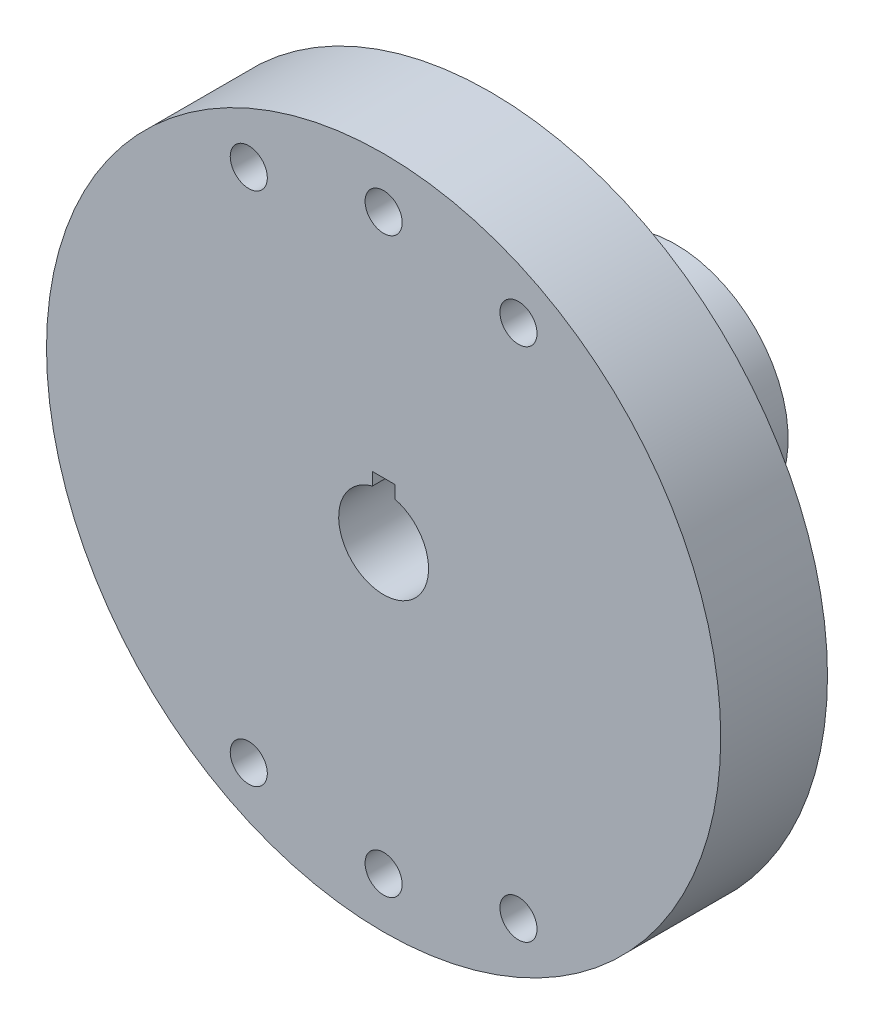
SolidWorks part; units mm, degrees
ref_plane "Front Plane" through (0, 0, 0) normal (0, 0, 1) x (1, 0, 0)
ref_plane "Top Plane" through (0, 0, 0) normal (0, 1, 0) x (1, 0, 0)
ref_plane "Right Plane" through (0, 0, 0) normal (1, 0, 0) x (0, 0, -1)
ref_plane "Plane1" through (0, 0, 0) normal (0, -1, 0) x (1, 0, 0)
sketch "Sketch1" plane through (0, 0, 0) normal (0, -1, 0) x (1, 0, 0)
  line L0 (30, 10) -> (0, 10)
  line L1 (0, 10) -> (0, 0.5)
  line L2 (0, 0.5) -> (30, 0.5)
  line L3 (30, 0.5) -> (30, 10)
  line L4 (0, 10) -> (0, 0.5) construction
revolve "Revolve1" add sketch "Sketch1" angle 360 about L4
sketch "Sketch2" plane through (0, 0, 0.5) normal (0, 0, -1) x (-1, 0, 0)
  arc A0 (1.9019, -26.9329) -> (10.5623, -24.8483) centre (0, 0) ccw
  arc A1 (10.5623, -24.8483) -> (14.3793, -22.8525) centre (12, -22.95) ccw
  arc A2 (14.3793, -22.8525) -> (14.3793, 22.8525) centre (0, 0) ccw
  arc A3 (14.3793, 22.8525) -> (10.5623, 24.8483) centre (12, 22.95) ccw
  arc A4 (10.5623, 24.8483) -> (1.9019, 26.9329) centre (0, 0) ccw
  arc A5 (1.9019, 26.9329) -> (-1.9019, 26.9329) centre (0, 25.5) ccw
  arc A6 (-1.9019, 26.9329) -> (-10.5623, 24.8483) centre (0, 0) ccw
  arc A7 (-10.5623, 24.8483) -> (-14.3793, 22.8525) centre (-12, 22.95) ccw
  arc A8 (-14.3793, 22.8525) -> (-14.3793, -22.8525) centre (0, 0) ccw
  arc A9 (-14.3793, -22.8525) -> (-10.5623, -24.8483) centre (-12, -22.95) ccw
  arc A10 (-10.5623, -24.8483) -> (-1.9019, -26.9329) centre (0, 0) ccw
  arc A11 (-1.9019, -26.9329) -> (1.9019, -26.9329) centre (0, -25.5) ccw
extrude "Cut-Extrude1" cut sketch "Sketch2" against normal blind 3.5
sketch "Sketch3" plane through (0, 0, 4) normal (0, 0, -1) x (-1, 0, 0)
  circle A0 centre (0, 0) radius 17.4
extrude "Boss-Extrude1" add sketch "Sketch3" along normal blind 4
sketch "Sketch4" plane through (0, 0, 0) normal (0, 0, -1) x (-1, 0, 0)
  circle A0 centre (0, 0) radius 10
extrude "Boss-Extrude2" add sketch "Sketch4" along normal blind 16
sketch "Sketch5" plane through (0, 0, 10) normal (0, 0, 1) x (1, 0, 0)
  line L0 (1, 5) -> (-1, 5)
  line L1 (-1, 5) -> (-1, 3.873)
  line L2 (1, 3.873) -> (1, 5)
  arc A0 (-1, 3.873) -> (1, 3.873) centre (0, 0) cw
extrude "Cut-Extrude2" cut sketch "Sketch5" against normal through all
sketch "Sketch6" plane through (0, 0, 0) normal (0, -1, 0) x (1, 0, 0)
  line L0 (4, 10) -> (0, 10)
  line L1 (0, 10) -> (0, -16)
  line L2 (0, -16) -> (4, -16)
  line L3 (4, -16) -> (4, 10)
  line L4 (0, 10) -> (0, -16) construction
revolve "Cut-Revolve1" cut sketch "Sketch6" angle 360 about L4
hole_wizard "#4 Clearance Hole1" positions "Sketch8" profile "Sketch7" hole size "#4" standard "ANSI Inch"
sketch "Sketch8" plane through (0, 0, 4) normal (0, 0, -1) x (-1, 0, 0)
  point P0 (12, -22.95)
  point P1 (0, -25.5)
  point P2 (-12, -22.95)
  point P3 (-12, 22.95)
  point P4 (0, 25.5)
  point P5 (12, 22.95)
sketch "Sketch7" plane through (-12, -22.95, 4) normal (1, 0, 0) x (0, 1, 0)
  line L0 (0, 0) -> (0, 6)
  line L1 (0, 6) -> (1.65, 6)
  line L2 (1.65, 6) -> (1.65, 0)
  line L5 (1.65, 0) -> (0, 0)
  line L11 (0, -6.35) -> (0, 107.95) construction
  dimension "Thru Hole Dia." = 3.3
  dimension "Thru Hole Depth" = 6
hole_wizard "#2 Clearance Hole1" positions "Sketch10" profile "Sketch9" hole size "#2" standard "ANSI Inch"
sketch "Sketch10" plane through (0, 0, -16) normal (0, 0, -1) x (-1, 0, 0)
  point P0 (-5.0558, -5.0558)
  point P1 (5.0558, -5.0558)
  point P2 (5.0558, 5.0558)
  point P3 (-5.0558, 5.0558)
sketch "Sketch9" plane through (5.0558, -5.0558, -16) normal (1, 0, 0) x (0, 1, 0)
  line L0 (0, 0) -> (0, 12)
  line L1 (0, 12) -> (1.25, 12)
  line L2 (1.25, 12) -> (1.25, 0)
  line L5 (1.25, 0) -> (0, 0)
  line L10 (0, 12) -> (-1.25, 12) construction
  line L11 (0, -6.35) -> (0, 107.95) construction
  dimension "Hole Dia." = 2.5
  dimension "Hole Depth" = 12
  dimension "Drill Angle" = 180
hole_wizard "#2 Clearance Hole2" positions "3DSketch1" profile "Sketch11" hole size "#2" standard "ANSI Inch"
sketch3d "3DSketch1"
  point P0 (0, -10, -6.2763)
sketch "Sketch11" plane through (0, -10, -6.2763) normal (1, 0, 0) x (0, 0, -1)
  line L0 (0, 0) -> (0, 6)
  line L1 (0, 6) -> (1.25, 6)
  line L2 (1.25, 6) -> (1.25, 0)
  line L5 (1.25, 0) -> (0, 0)
  line L11 (0, -6.35) -> (0, 107.95) construction
  dimension "Thru Hole Dia." = 2.5
  dimension "Thru Hole Depth" = 6
hole_wizard "#2 Clearance Hole3" positions "3DSketch2" profile "Sketch12" hole size "#2" standard "ANSI Inch"
sketch3d "3DSketch2"
  point P0 (0, 10, -6.2763)
sketch "Sketch12" plane through (0, 10, -6.2763) normal (1, 0, 0) x (0, 0, 1)
  line L0 (0, 0) -> (0, 40)
  line L1 (0, 40) -> (1.5, 40)
  line L2 (1.5, 40) -> (1.5, 0)
  line L5 (1.5, 0) -> (0, 0)
  line L11 (0, -6.35) -> (0, 107.95) construction
  dimension "Thru Hole Dia." = 3
  dimension "Thru Hole Depth" = 40
fillet "Fillet1" radius 3 1 edges at (-10, 0, 0)
pattern_circular "阵列(圆周)1" count 2 every 90 about axis through (0, 0, -16) along (0, 0, -1) of "#2 Clearance Hole3"
